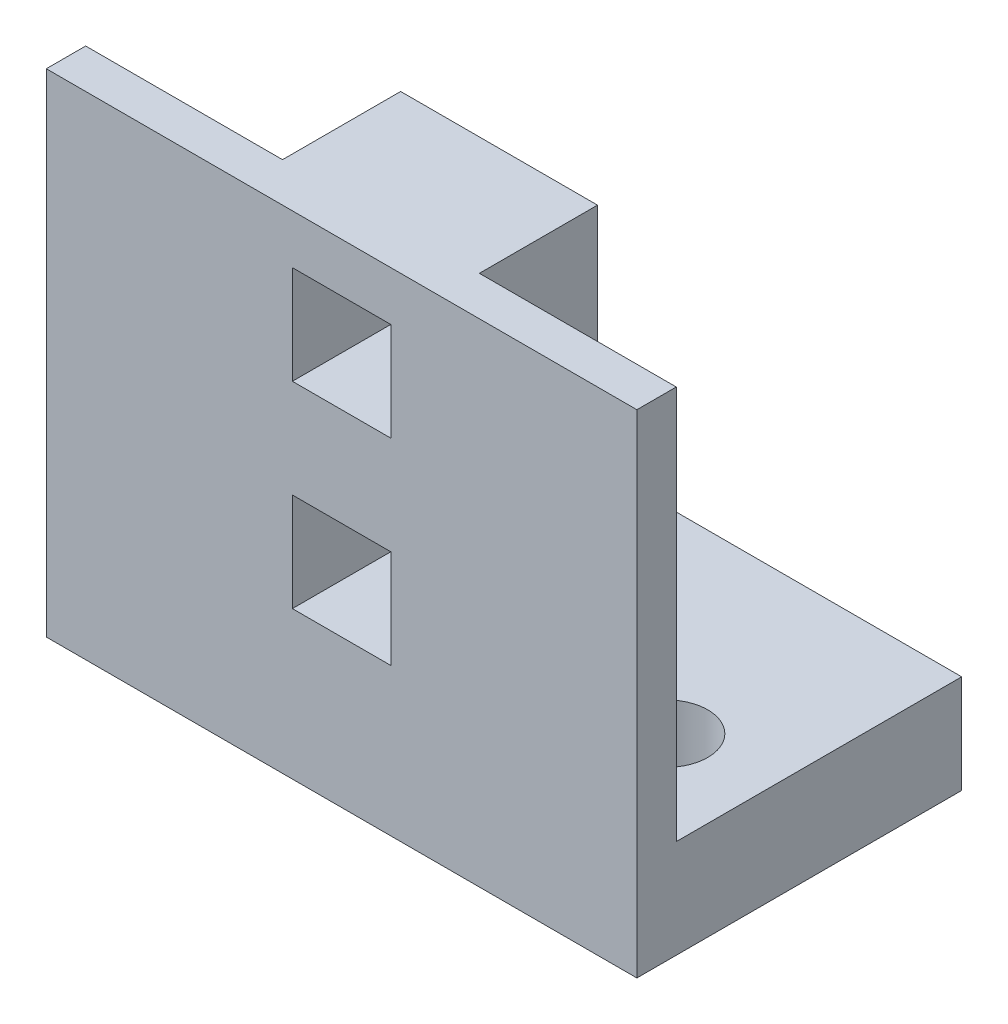
SolidWorks part; units mm, degrees
ref_plane "Front Plane" through (0, 0, 0) normal (0, 0, 1) x (1, 0, 0)
ref_plane "Top Plane" through (0, 0, 0) normal (0, 1, 0) x (1, 0, 0)
ref_plane "Right Plane" through (0, 0, 0) normal (1, 0, 0) x (0, 0, -1)
sketch "Sketch1" plane through (0, 0, 0) normal (0, 1, 0) x (1, 0, 0)
  line L1 (-15, 8.25) -> (15, 8.25)
  line L2 (-15, 8.25) -> (-15, -8.25)
  line L3 (-15, -8.25) -> (15, -8.25)
  line L4 (15, 8.25) -> (15, -8.25)
  line L5 (-15, 8.25) -> (15, -8.25) construction
  line L6 (-15, -8.25) -> (15, 8.25) construction
  circle A0 centre (-10, -1.75) radius 2.1
  circle A1 centre (10, -1.75) radius 2.1
  point P0 (0, 0)
  dimension "D3" = 10
  dimension "D4" = 10
  dimension "D5" = 5
  dimension "D7" = 4.2
  dimension "D8" = 4.2
  dimension "D1" = 16.5
  dimension "D2" = 30
  dimension "D6" = 5
extrude "Boss-Extrude1" add sketch "Sketch1" along normal blind 5
sketch "Sketch2" plane through (0, 0, 8.25) normal (0, 0, 1) x (1, 0, 0)
  line L1 (-15, 5) -> (15, 5)
  line L2 (-15, 5) -> (-15, 25)
  line L3 (-15, 25) -> (15, 25)
  line L4 (15, 5) -> (15, 25)
  dimension "D1" = 20
extrude "Boss-Extrude2" add sketch "Sketch2" against normal blind 2
sketch "Sketch3" plane through (0, 0, 6.25) normal (0, 0, -1) x (-1, 0, 0)
  line L0 (15, 5) -> (-15, 5) construction
  line L9 (-2.5, 7.5) -> (2.5, 7.5)
  line L10 (-2.5, 7.5) -> (-2.5, 12.5)
  line L11 (-2.5, 12.5) -> (2.5, 12.5)
  line L12 (2.5, 7.5) -> (2.5, 12.5)
  line L13 (-2.5, 17.5) -> (2.5, 17.5)
  line L14 (-2.5, 17.5) -> (-2.5, 22.5)
  line L15 (-2.5, 22.5) -> (2.5, 22.5)
  line L16 (2.5, 17.5) -> (2.5, 22.5)
  line L17 (-15, 25) -> (15, 25) construction
  line L18 (-15, 5) -> (-15, 25) construction
  line L19 (15, 25) -> (15, 5) construction
  dimension "D1" = 5
  dimension "D2" = 5
  dimension "D3" = 5
  dimension "D4" = 5
  dimension "D5" = 5
  dimension "D6" = 2.5
  dimension "D7" = 2.5
  dimension "D8" = 12.5
  dimension "D9" = 12.5
  dimension "D10" = 12.5
extrude "Cut-Extrude1" cut sketch "Sketch3" against normal through all
sketch "Sketch4" plane through (0, 0, 6.25) normal (0, 0, -1) x (-1, 0, 0)
  line L0 (-15, 25) -> (15, 25) construction
  line L1 (-5, 25) -> (5, 25)
  line L2 (-5, 25) -> (-5, 5)
  line L3 (-5, 5) -> (5, 5)
  line L4 (5, 25) -> (5, 5)
  line L5 (-15, 5) -> (15, 5) construction
  line L6 (-15, 5) -> (-15, 25) construction
  line L7 (15, 25) -> (15, 5) construction
  line L9 (-2.5, 22.5) -> (2.5, 22.5)
  line L10 (-2.5, 22.5) -> (-2.5, 17.5)
  line L11 (-2.5, 17.5) -> (2.5, 17.5)
  line L12 (2.5, 22.5) -> (2.5, 17.5)
  line L13 (-2.5, 12.5) -> (2.5, 12.5)
  line L14 (-2.5, 12.5) -> (-2.5, 7.5)
  line L15 (-2.5, 7.5) -> (2.5, 7.5)
  line L16 (2.5, 12.5) -> (2.5, 7.5)
  dimension "D1" = 10
  dimension "D2" = 10
extrude "Boss-Extrude3" add sketch "Sketch4" along normal blind 4
sketch "Sketch5" plane through (0, 0, 2.25) normal (0, 0, -1) x (-1, 0, 0)
  line L1 (-5, 25) -> (5, 25)
  line L2 (-5, 25) -> (-5, 5)
  line L3 (-5, 5) -> (5, 5)
  line L4 (5, 25) -> (5, 5)
extrude "Boss-Extrude4" add sketch "Sketch5" along normal blind 2
